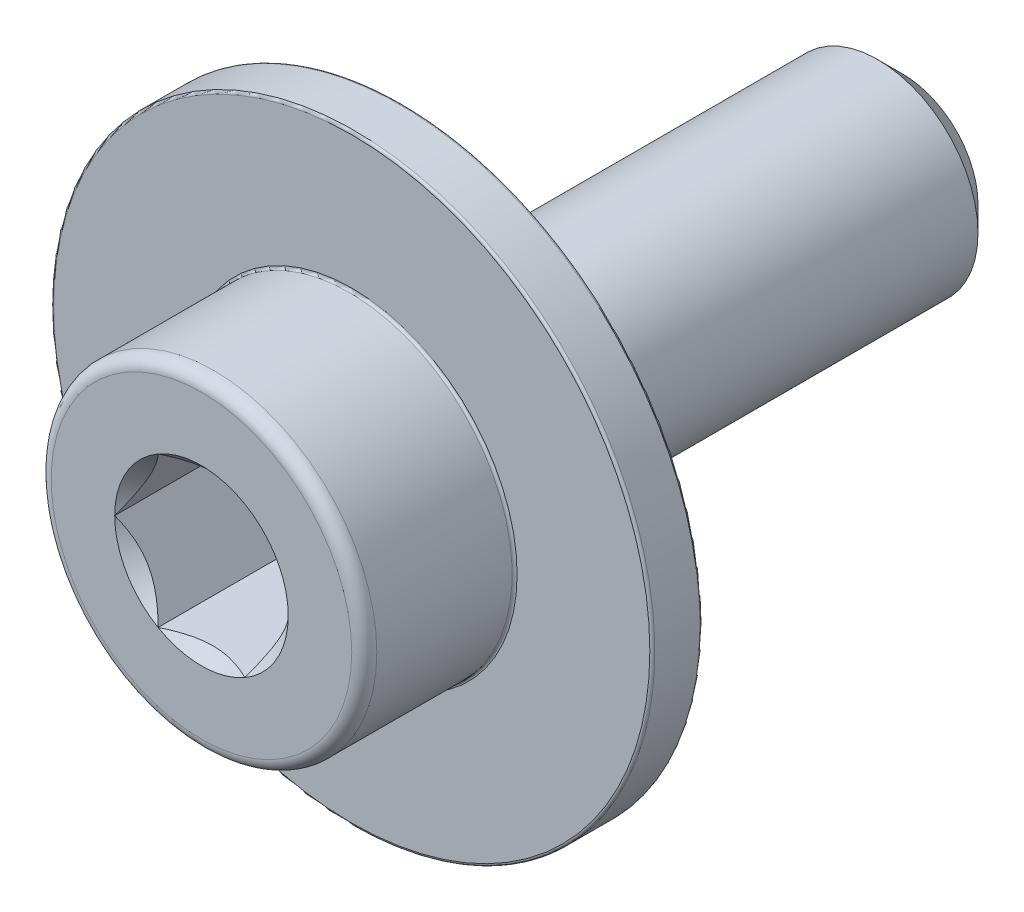
SolidWorks part; units mm, degrees
material "Acciaio inossidabile (ferroso)"
ref_plane "Piano frontale" through (0, 0, 0) normal (0, 0, 1) x (1, 0, 0)
ref_plane "Piano superiore" through (0, 0, 0) normal (0, 1, 0) x (1, 0, 0)
ref_plane "Piano destro" through (0, 0, 0) normal (1, 0, 0) x (0, 0, -1)
sketch "Schizzo1" plane through (0, 0, 0) normal (0, 0, 1) x (1, 0, 0)
  circle A0 centre (0, 0) radius 4
  dimension "D1" = 8
extrude "Estrusione-Estrusione1" add sketch "Schizzo1" along normal blind 20
cosmetic thread "Filettatura cosmetica2" parameters "D2"=6.619
chamfer "Smusso1" distance 1 angle 45 1 edges at (4, 0, 0)
sketch "Schizzo6" plane through (0, 0, 20) normal (0, 0, 1) x (1, 0, 0)
  circle A0 centre (0, 0) radius 6.5
  dimension "D1" = 13
extrude "Estrusione-Estrusione3" add sketch "Schizzo6" along normal blind 8
sketch "Schizzo7" plane through (0, 0, 28) normal (0, 0, 1) x (1, 0, 0)
  line L1 (1.7321, 3) -> (-1.7321, 3)
  line L2 (-1.7321, 3) -> (-3.4641, 0)
  line L3 (-3.4641, 0) -> (-1.7321, -3)
  line L4 (-1.7321, -3) -> (1.7321, -3)
  line L5 (1.7321, -3) -> (3.4641, 0)
  line L6 (3.4641, 0) -> (1.7321, 3)
  circle A1 centre (0, 0) radius 3 construction
  dimension "D1" = 6
extrude "Taglio-Estrusione3" cut sketch "Schizzo7" against normal blind 6
sketch "Schizzo8" plane through (0, 0, 28) normal (0, 0, 1) x (1, 0, 0)
  circle A0 centre (0, 0) radius 3.4641
extrude "Taglio-Estrusione4" cut sketch "Schizzo8" against normal blind 1 draft 45
fillet "Raccordo1" radius 0.5 1 edges at (6.5, 0, 28)
sketch "Schizzo9" plane through (0, 0, 20) normal (0, 0, -1) x (-1, 0, 0)
  circle A0 centre (0, 0) radius 6.5
  circle A1 centre (0, 0) radius 12
  dimension "D1" = 13
  dimension "D2" = 24
extrude "Estrusione-Estrusione4" add sketch "Schizzo9" against normal blind 2
fillet "Raccordo2" radius 0.1 3 edges at (-12, 0, 22) (-6.5, 0, 22) (-12, 0, 20)
